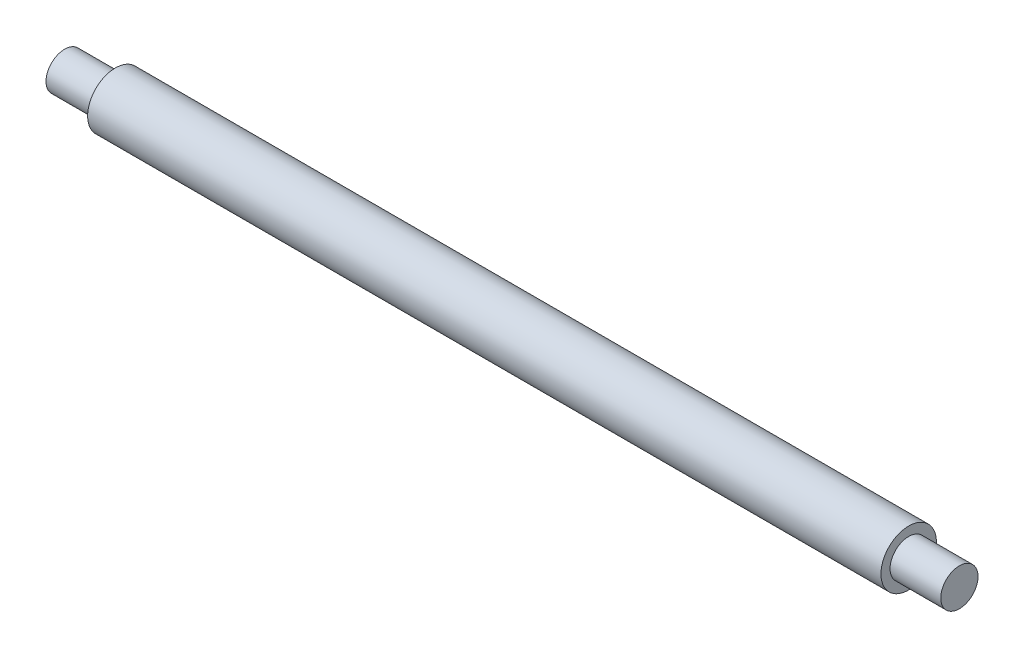
SolidWorks part; units mm, degrees
ref_plane "Front Plane" through (0, 0, 0) normal (0, 0, 1) x (1, 0, 0)
ref_plane "Top Plane" through (0, 0, 0) normal (0, 1, 0) x (1, 0, 0)
ref_plane "Right Plane" through (0, 0, 0) normal (1, 0, 0) x (0, 0, -1)
sketch "Sketch1" plane through (0, 0, 0) normal (0, 0, 1) x (1, 0, 0)
  line L0 (0, 0) -> (27.6586, 0) construction
  line L1 (0, 0) -> (0, 10.598) construction
  line L2 (76.2, 0) -> (76.2, 3.175)
  line L3 (76.2, 3.175) -> (67.564, 3.175)
  line L4 (67.564, 3.175) -> (67.564, 4.7244)
  line L5 (67.564, 4.7244) -> (-67.564, 4.7244)
  line L6 (-76.2, 0) -> (76.2, 0)
  line L7 (-76.2, 0) -> (-76.2, 3.175)
  line L8 (-76.2, 3.175) -> (-67.564, 3.175)
  line L9 (-67.564, 3.175) -> (-67.564, 4.7244)
  line L10 (0, 0) -> (39.0474, 0) construction
  point P13 (0, 4.7244)
  dimension "D1" = 9.4488
  dimension "D2" = 8.636
  dimension "D3" = 6.35
  dimension "D4" = 152.4
revolve "Revolve1" add sketch "Sketch1" angle 360 about L6
cosmetic thread "Cosmetic Thread3"
cosmetic thread "Cosmetic Thread4"
